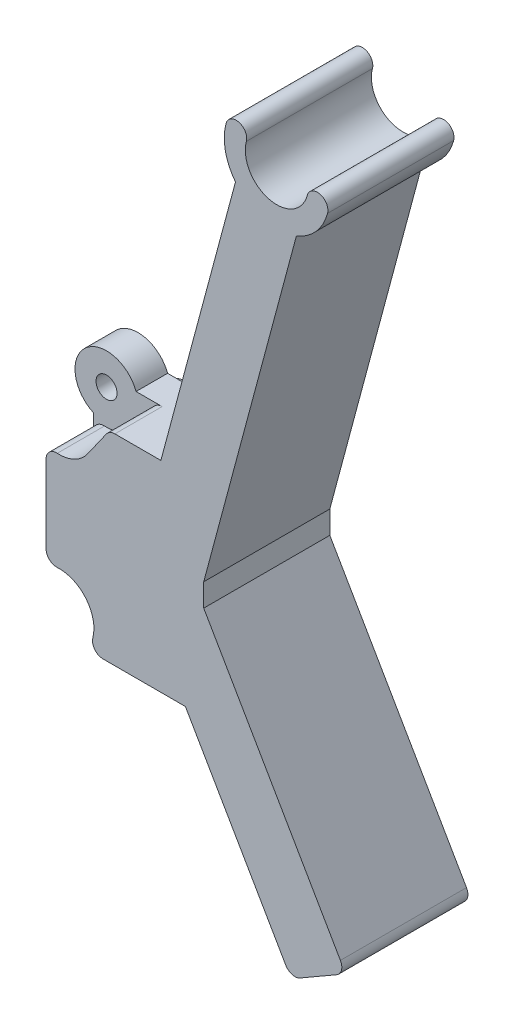
SolidWorks part; units mm, degrees
ref_plane "Front Plane" through (0, 0, 0) normal (0, 0, 1) x (1, 0, 0)
ref_plane "Top Plane" through (0, 0, 0) normal (0, 1, 0) x (1, 0, 0)
ref_plane "Right Plane" through (0, 0, 0) normal (1, 0, 0) x (0, 0, -1)
sketch "Sketch1" plane through (0, 0, 0) normal (0, 0, 1) x (1, 0, 0)
  line L0 (-5.3086, 12.707) -> (-5.3086, 23.2526)
  line L1 (-1.2478, 27.0282) -> (5.6132, 27.0282)
  line L2 (5.6132, 27.0282) -> (12.7142, 53.5296)
  line L3 (18.5098, 51.9767) -> (9.6914, 19.0658)
  line L7 (-4.0586, 25.9798) -> (-4.0586, 9.9798) construction
  line L8 (9.6914, 19.0658) -> (9.6914, 16.8938)
  line L9 (9.6914, 16.8938) -> (23.1983, -6.501)
  line L10 (-1.8833, 7.9139) -> (7.9477, 7.9139)
  line L11 (7.9477, 7.9139) -> (18.0022, -9.501)
  line L12 (18.0022, -9.501) -> (23.1983, -6.501)
  line L13 (5.6132, 27.5608) -> (5.6132, 50027.5608) construction
  line L14 (7.9477, 7.8459) -> (7.9477, -49992.1541) construction
  line L15 (-5.3086, 17.9798) -> (9.6914, 17.9798) construction
  line L16 (20.6002, -8.001) -> (5.6002, 17.9798) construction
  line L17 (16.6473, 56.6168) -> (6.2945, 17.9798) construction
  line L18 (12.7836, 57.6521) -> (20.511, 55.5816) construction
  arc A0 (-5.3086, 23.2526) -> (-1.2478, 27.0282) centre (-4.0586, 25.9798) cw
  arc A1 (-5.3086, 12.707) -> (-1.8833, 7.9139) centre (-4.0586, 9.9798) ccw
  arc A2 (12.7142, 53.5296) -> (11.8177, 57.9109) centre (16.6473, 56.6168) cw
  arc A3 (11.8177, 57.9109) -> (13.7495, 57.3933) centre (12.7836, 57.6521) cw
  arc A4 (13.7495, 57.3933) -> (19.5451, 55.8404) centre (16.6473, 56.6168) ccw
  arc A5 (19.5451, 55.8404) -> (21.4769, 55.3227) centre (20.511, 55.5816) cw
  arc A6 (21.4769, 55.3227) -> (18.5098, 51.9767) centre (16.6473, 56.6168) cw
  circle A7 centre (-4.0586, 25.9798) radius 1
  circle A8 centre (-4.0586, 9.9798) radius 1
  dimension "D1" = 3
  dimension "D2" = 2
  dimension "D10" = 5
  dimension "D11" = 3
  dimension "D3" = 16
  dimension "D4" = 15
  dimension "D5" = 6
  dimension "D6" = 6
  dimension "D7" = 15
  dimension "D8" = 30
  dimension "D9" = 2.5
  dimension "D12" = 40
  dimension "D13" = 30
extrude "Boss-Extrude1" add sketch "Sketch1" along normal blind 12
ref_plane "midplane" through (0, 0, 6) normal (0, 0, 1) x (1, 0, 0)
sketch "Sketch2" plane through (0, 0, 12) normal (0, 0, 1) x (1, 0, 0)
  line L0 (-1.3603, 24.0801) -> (2.3019, 29.2818)
  line L1 (2.3019, 29.2818) -> (-2.705, 28.9894)
  arc A0 (-2.705, 28.9894) -> (-1.3603, 24.0801) centre (-4.0586, 25.9798) ccw
  circle A1 centre (-4.0586, 9.9798) radius 3.3
  dimension "D1" = 6.6
extrude "Cut-Extrude1" cut sketch "Sketch2" against normal blind 4.5
mirror "Mirror1" about plane through (0, 0, 6) normal (0, 0, 1) of "Cut-Extrude1"
fillet "Fillet1" radius 1 8 edges at (-1.4853, 7.9139, 9.75) (-1.4853, 7.9139, 2.25) (-5.3086, 13.0339, 2.25) (-5.3086, 13.0339, 9.75) (-5.3086, 22.9257, 2.25) (-5.3086, 22.9257, 9.75) (0.7153, 27.0282, 2.25) (0.7153, 27.0282, 9.75)
fillet "Fillet2" radius 1 2 edges at (18.0022, -9.501, 6) (23.1983, -6.501, 6)
equation "\"axle-diameter\"=2"
equation "\"switch-thickness\"=12"
equation "\"base-width\"=6"
equation "\"axle-bushing-radius\"=3"
equation "\"D2@Sketch1\"=\"axle-diameter\""
equation "\"D1@Sketch1\"=\"axle-bushing-radius\""
equation "\"D1@Boss-Extrude1\"=\"switch-thickness\""
equation "\"D5@Sketch1\"=\"base-width\""
equation "\"D6@Sketch1\"=\"base-width\""
equation "\"D1@Sketch2\"=\"axle-bushing-radius\"*2.2"
equation "\"D1@Cut-Extrude1\"=\"switch-thickness\"/3+\"clearance\""
equation "\"clearance\"= 0.5"
